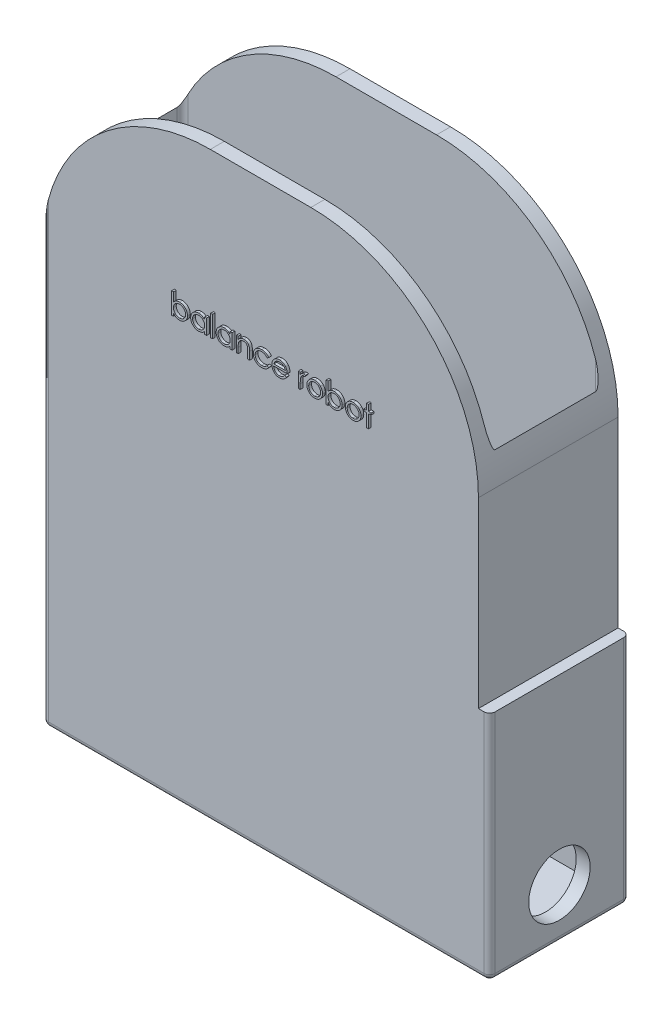
SolidWorks part; units mm, degrees
material "Cam"
ref_plane "Ön Düzlem" through (0, 0, 0) normal (0, 0, 1) x (1, 0, 0)
ref_plane "Üst Düzlem" through (0, 0, 0) normal (0, 1, 0) x (1, 0, 0)
ref_plane "Sağ Düzlem" through (0, 0, 0) normal (1, 0, 0) x (0, 0, -1)
sketch "Çizim1" plane through (0, 0, 0) normal (0, 1, 0) x (1, 0, 0)
  line L1 (-75, -20) -> (75, -20)
  line L2 (-75, -20) -> (-75, 20)
  line L3 (-75, 20) -> (75, 20)
  line L4 (75, -20) -> (75, 20)
  line L5 (-75, -20) -> (75, 20) construction
  line L6 (-75, 20) -> (75, -20) construction
  line L7 (-80, -25) -> (80, -25)
  line L8 (-80, -25) -> (-80, 25)
  line L9 (-80, 25) -> (80, 25)
  line L10 (80, -25) -> (80, 25)
  line L11 (-80, -25) -> (80, 25) construction
  line L12 (-80, 25) -> (80, -25) construction
  point P0 (0, 0)
  point P6 (0, 0)
  dimension "D1" = 150
  dimension "D2" = 40
  dimension "D3" = 160
  dimension "D4" = 50
extrude "Yükseklik-Ekstrüzyon1" add sketch "Çizim1" along normal blind 260
sketch "Çizim3" plane through (0, 0, 0) normal (0, -1, 0) x (1, 0, 0)
  line L1 (80, -25) -> (-80, -25)
  line L2 (80, -25) -> (80, 25)
  line L3 (80, 25) -> (-80, 25)
  line L4 (-80, -25) -> (-80, 25)
extrude "Yükseklik-Ekstrüzyon2" add sketch "Çizim3" along normal blind 5
sketch "Çizim4" plane through (80, 0, 0) normal (1, 0, 0) x (0, 0, -1)
  line L0 (25, -5) -> (-25, -5) construction
  circle A0 centre (0, 13) radius 11
  dimension "D1" = 18
extrude "Kes-Ekstrüzyon1" cut sketch "Çizim4" against normal blind 248
fillet "Radyus1" radius 2 21 edges at (-80, 127.5, 25) (-75, 130, -20) (80, 127.5, 25) (80, 127.5, -25) (-80, -5, 0) (80, -5, 0) (0, -5, 25) (0, -5, -25) (-75, 260, 0) (0, 260, 20) (0, 260, -20) (75, 260, 0) (80, 260, 0) (-80, 260, 0) (0, 0, 20) (0, 260, -25) (0, 260, 25) (-80, 127.5, -25) (-75, 130, 20) (75, 130, -20) (75, 130, 20)
ref_plane "Düzlem1" through (0, 50, 0) normal (0, 1, 0) x (1, 0, 0)
sketch "Çizim5" plane through (0, 50, 0) normal (0, 1, 0) x (1, 0, 0)
  line L4 (73, 20) -> (-73, 20)
  line L5 (-75, 18) -> (-75, -18)
  line L6 (-75, -18) -> (75, -18)
  line L7 (75, -18) -> (75, 18)
  line L8 (73, 20) -> (-73, 20)
  line L9 (-75, 18) -> (-75, -18)
  line L10 (-75, -18) -> (75, -18)
  line L11 (75, -18) -> (75, 18)
  arc A1 (-73, 20) -> (-75, 18) centre (-73, 18) ccw
  arc A2 (-73, 20) -> (-75, 18) centre (-73, 18) ccw
  arc A4 (75, 18) -> (73, 20) centre (73, 18) ccw
  arc A5 (75, 18) -> (73, 20) centre (73, 18) ccw
  dimension "D1" = 0
extrude "Yükseklik-Ekstrüzyon3" add sketch "Çizim5" along normal blind 10
sketch "Çizim6" plane through (0, 0, 25) normal (0, 0, 1) x (1, 0, 0)
  line L10 (-88.596, 275.0645) -> (92.445, 275.0645)
  line L11 (-80.002, 78.1066) -> (-80.002, 143.4989)
  line L12 (-20.002, 203.4989) -> (15.998, 203.4989)
  line L13 (75.998, 78.1066) -> (75.998, 143.4989)
  line L14 (-80.002, 78.1066) -> (-97.19, 78.1066)
  line L15 (-97.19, 78.1066) -> (-97.19, 210.0367)
  line L16 (-97.19, 210.0367) -> (-88.596, 275.0645)
  line L17 (92.445, 275.0645) -> (92.445, 78.1066)
  line L18 (92.445, 78.1066) -> (75.998, 78.1066)
  arc A2 (75.998, 143.4989) -> (15.998, 203.4989) centre (15.998, 143.4989) ccw
  arc A3 (-20.002, 203.4989) -> (-80.002, 143.4989) centre (-20.002, 143.4989) ccw
  point P9 (78, 260)
  dimension "D2" = 60
extrude "Kes-Ekstrüzyon2" cut sketch "Çizim6" against normal blind 76
sketch "Çizim8" plane through (0, 0, 25) normal (0, 0, 1) x (1, 0, 0)
  text T0 "balance robot" font "Century Gothic" height in points 28
extrude "Yükseklik-Ekstrüzyon4" add sketch "Çizim8" along normal blind 1
